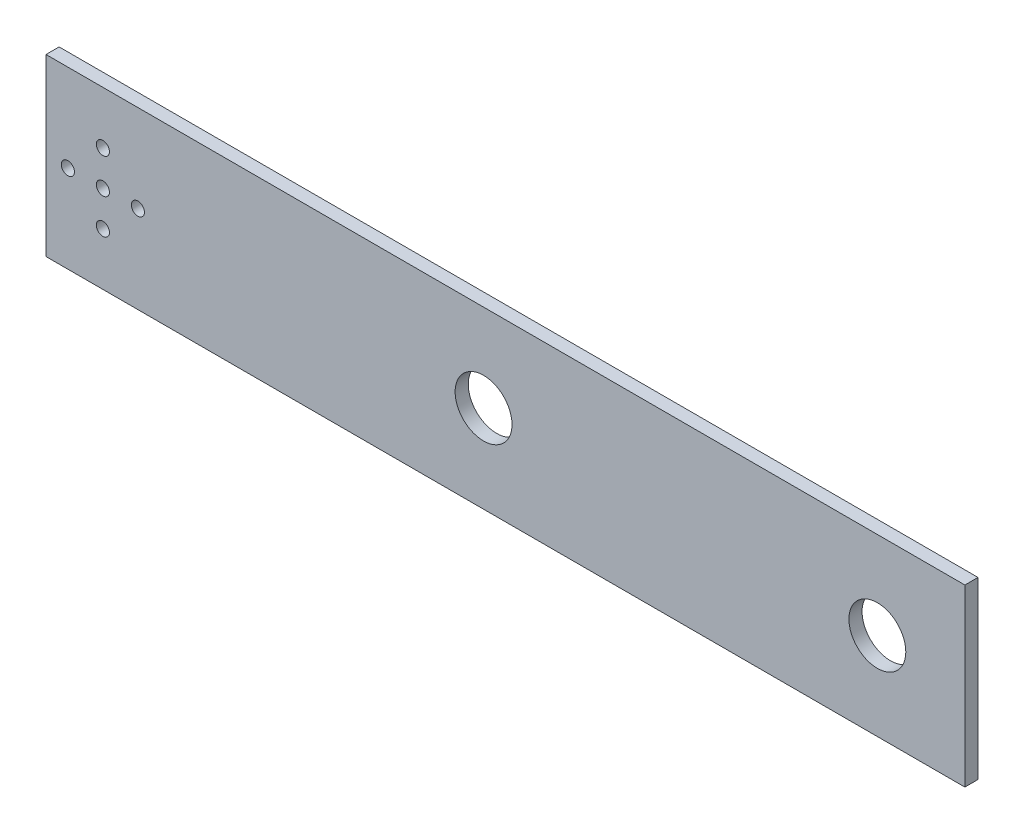
SolidWorks part; units mm, degrees
material "1060 Alloy"
ref_plane "Front Plane" through (0, 0, 0) normal (0, 0, 1) x (1, 0, 0)
ref_plane "Top Plane" through (0, 0, 0) normal (0, 1, 0) x (1, 0, 0)
ref_plane "Right Plane" through (0, 0, 0) normal (1, 0, 0) x (0, 0, -1)
sketch "Sketch1" plane through (0, 0, 0) normal (0, 0, 1) x (1, 0, 0)
  line L0 (-10, 20) -> (200, 20)
  line L1 (-10, -20) -> (200, -20)
  line L2 (200, -20) -> (200, 20)
  line L3 (-10, 20) -> (-10, -20)
  circle A1 centre (0, 8) radius 1.25
  circle A2 centre (8, 0) radius 1.25
  circle A3 centre (0, -8) radius 1.25
  circle A4 centre (-8, 0) radius 1.25
  point P16 (0, 0)
  dimension "D2" = 210
  dimension "D3" = 40
  dimension "D1" = 4
extrude "Boss-Extrude1" add sketch "Sketch1" along normal blind 3 separate body contours L0 L2 L1 L3
hole_wizard "Ø3.0 (3) Diameter Hole2" positions "Sketch5" profile "Sketch4" hole size "Ø3.0" standard "ISO" end condition through all
sketch "Sketch5" plane through (0, 0, 0) normal (0, 0, -1) x (-1, 0, 0)
  line L1 (10, 20) -> (10, -20) construction
  point P0 (-3, 8)
  point P3 (-11, 0)
  point P6 (5, 0)
  point P9 (-3, -8)
  point P21 (-3, 0)
  point P32 (10, 0)
  dimension "D1" = 16
  dimension "D2" = 8
  dimension "D3" = 5
  dimension "D4" = 8
  dimension "D5" = 8
  dimension "D6" = 8
sketch "Sketch4" plane through (3, 8, 0) normal (1, 0, 0) x (0, 1, 0)
  line L0 (0, 0) -> (0, 3)
  line L1 (0, 3) -> (1.5, 3)
  line L2 (1.5, 3) -> (1.5, 0)
  line L5 (1.5, 0) -> (0, 0)
  line L11 (0, -6.35) -> (0, 107.95) construction
  dimension "Thru Hole Dia." = 3
  dimension "Thru Hole Depth" = 3
hole_wizard "Ø13.0 (13) Diameter Hole1" positions "Sketch7" profile "Sketch6" hole size "Ø13.0" standard "ISO" end condition through all
sketch "Sketch7" plane through (0, 0, 3) normal (0, 0, 1) x (1, 0, 0)
  line L0 (-10, 20) -> (-10, -20) construction
  line L1 (-10, 20) -> (200, 20) construction
  line L2 (-10, 20) -> (-10, -20) construction
  point P0 (90, 0)
  point P2 (180, 0)
  point P5 (-10, 0)
  point P10 (-10, 0)
  dimension "D1" = 100
  dimension "D2" = 20
  dimension "D3" = 20
  dimension "D4" = 190
sketch "Sketch6" plane through (90, 0, 3) normal (1, 0, 0) x (0, -1, 0)
  line L0 (0, 0) -> (0, 3)
  line L1 (0, 3) -> (6.5, 3)
  line L2 (6.5, 3) -> (6.5, 0)
  line L5 (6.5, 0) -> (0, 0)
  line L11 (0, -6.35) -> (0, 107.95) construction
  dimension "Thru Hole Dia." = 13
  dimension "Thru Hole Depth" = 3
